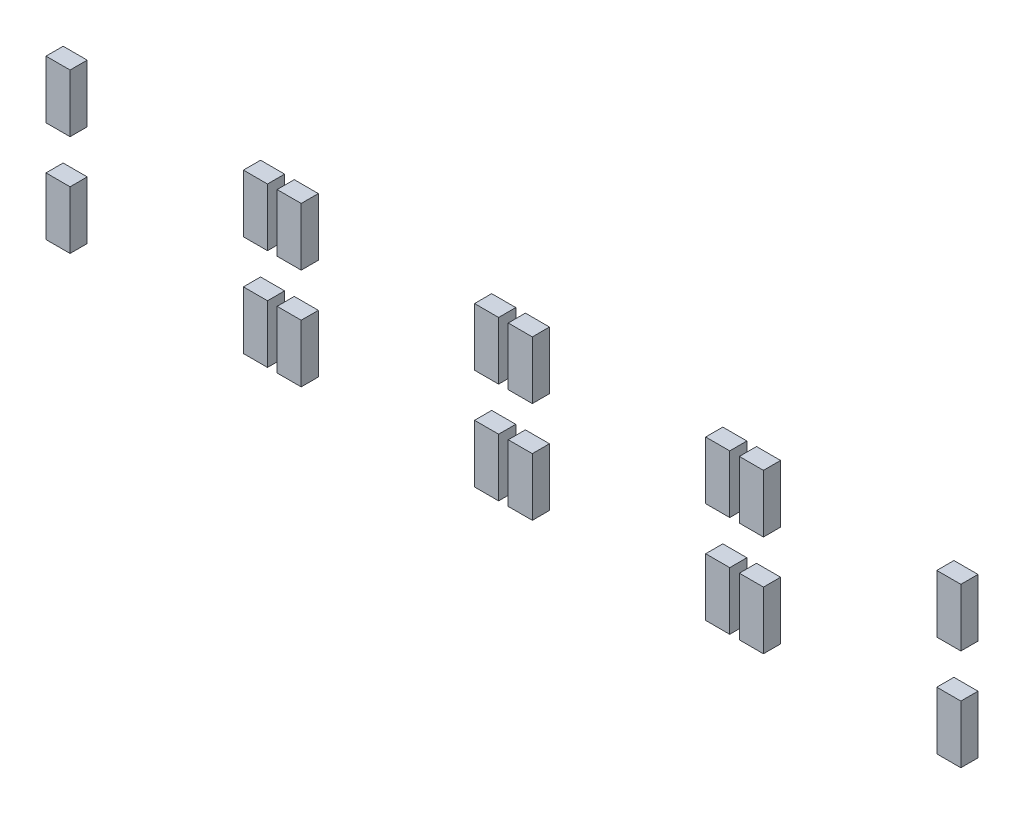
SolidWorks part; units mm, degrees
ref_plane "Front Plane" through (0, 0, 0) normal (0, 0, 1) x (1, 0, 0)
ref_plane "Top Plane" through (0, 0, 0) normal (0, 1, 0) x (1, 0, 0)
ref_plane "Right Plane" through (0, 0, 0) normal (1, 0, 0) x (0, 0, -1)
ref_plane "Plane4" through (0, 0, -1.5875) normal (0, 0, 1) x (1, 0, 0)
sketch "Sketch11" plane through (0, 0, -1.5875) normal (0, 0, 1) x (1, 0, 0)
  line L0 (25.5, -42) -> (23, -42)
  line L1 (5, -42) -> (2.5, -42)
  line L2 (5, -42) -> (5, -48)
  line L3 (5, -48) -> (2.5, -48)
  line L4 (2.5, -42) -> (2.5, -48)
  line L5 (25.5, -42) -> (25.5, -48)
  line L6 (25.5, -48) -> (23, -48)
  line L7 (23, -42) -> (23, -48)
  line L8 (5, -52.5) -> (2.5, -52.5)
  line L9 (5, -52.5) -> (5, -58.5)
  line L10 (5, -58.5) -> (2.5, -58.5)
  line L11 (2.5, -52.5) -> (2.5, -58.5)
  line L12 (25.5, -52.5) -> (23, -52.5)
  line L13 (25.5, -52.5) -> (25.5, -58.5)
  line L14 (25.5, -58.5) -> (23, -58.5)
  line L15 (23, -52.5) -> (23, -58.5)
  line L16 (49.5, -42) -> (47, -42)
  line L17 (29, -42) -> (26.5, -42)
  line L18 (29, -42) -> (29, -48)
  line L19 (29, -48) -> (26.5, -48)
  line L20 (26.5, -42) -> (26.5, -48)
  line L21 (49.5, -42) -> (49.5, -48)
  line L22 (49.5, -48) -> (47, -48)
  line L23 (47, -42) -> (47, -48)
  line L24 (29, -52.5) -> (26.5, -52.5)
  line L25 (29, -52.5) -> (29, -58.5)
  line L26 (29, -58.5) -> (26.5, -58.5)
  line L27 (26.5, -52.5) -> (26.5, -58.5)
  line L28 (49.5, -52.5) -> (47, -52.5)
  line L29 (49.5, -52.5) -> (49.5, -58.5)
  line L30 (49.5, -58.5) -> (47, -58.5)
  line L31 (47, -52.5) -> (47, -58.5)
  line L32 (73.5, -42) -> (71, -42)
  line L33 (53, -42) -> (50.5, -42)
  line L34 (53, -42) -> (53, -48)
  line L35 (53, -48) -> (50.5, -48)
  line L36 (50.5, -42) -> (50.5, -48)
  line L37 (73.5, -42) -> (73.5, -48)
  line L38 (73.5, -48) -> (71, -48)
  line L39 (71, -42) -> (71, -48)
  line L40 (53, -52.5) -> (50.5, -52.5)
  line L41 (53, -52.5) -> (53, -58.5)
  line L42 (53, -58.5) -> (50.5, -58.5)
  line L43 (50.5, -52.5) -> (50.5, -58.5)
  line L44 (73.5, -52.5) -> (71, -52.5)
  line L45 (73.5, -52.5) -> (73.5, -58.5)
  line L46 (73.5, -58.5) -> (71, -58.5)
  line L47 (71, -52.5) -> (71, -58.5)
  line L48 (97.5, -42) -> (95, -42)
  line L49 (77, -42) -> (74.5, -42)
  line L50 (77, -42) -> (77, -48)
  line L51 (77, -48) -> (74.5, -48)
  line L52 (74.5, -42) -> (74.5, -48)
  line L53 (97.5, -42) -> (97.5, -48)
  line L54 (97.5, -48) -> (95, -48)
  line L55 (95, -42) -> (95, -48)
  line L56 (77, -52.5) -> (74.5, -52.5)
  line L57 (77, -52.5) -> (77, -58.5)
  line L58 (77, -58.5) -> (74.5, -58.5)
  line L59 (74.5, -52.5) -> (74.5, -58.5)
  line L60 (97.5, -52.5) -> (95, -52.5)
  line L61 (97.5, -52.5) -> (97.5, -58.5)
  line L62 (97.5, -58.5) -> (95, -58.5)
  line L63 (95, -52.5) -> (95, -58.5)
  dimension "D1" = 4
extrude "Boss-Extrude5" add sketch "Sketch11" against normal blind 1.78
